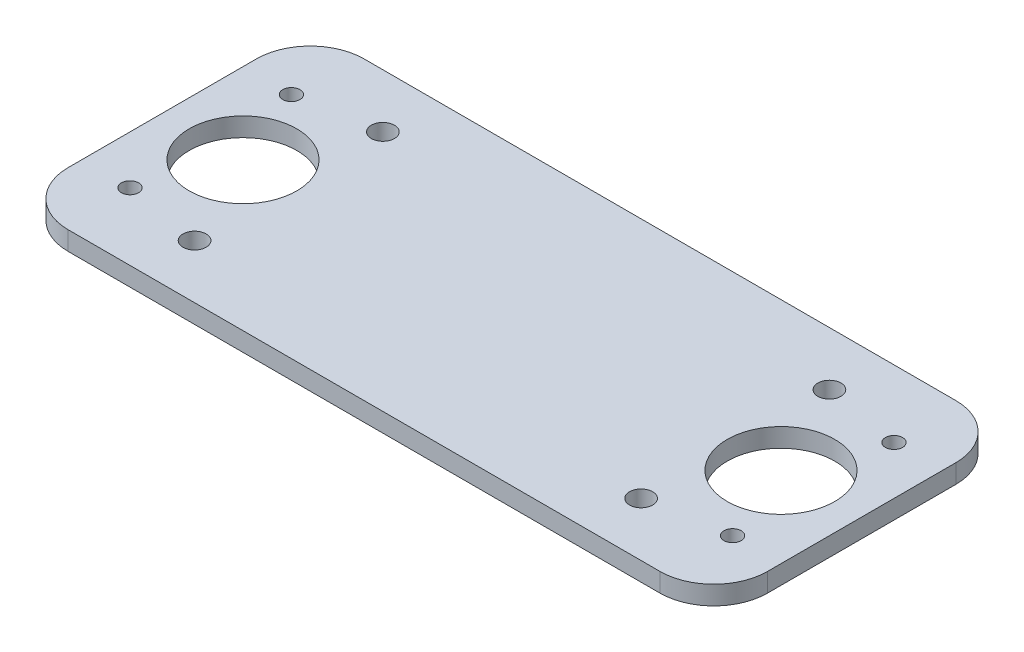
SolidWorks part; units mm, degrees
ref_plane "Front Plane" through (0, 0, 0) normal (0, 0, 1) x (1, 0, 0)
ref_plane "Top Plane" through (0, 0, 0) normal (0, 1, 0) x (1, 0, 0)
ref_plane "Right Plane" through (0, 0, 0) normal (1, 0, 0) x (0, 0, -1)
sketch "Sketch1" plane through (0, 0, 0) normal (0, 1, 0) x (1, 0, 0)
  line L0 (65, 20.185) -> (65, -60.6934) construction
  line L1 (0, 0) -> (130, 0)
  line L2 (0, 0) -> (0, -55)
  line L3 (0, -55) -> (130, -55)
  line L4 (130, 0) -> (130, -55)
  line L5 (-10.4412, -27.5) -> (139.8504, -27.5) construction
  circle A0 centre (9, -12.5) radius 1.6
  circle A1 centre (9, -42.5) radius 1.6
  circle A4 centre (121, -42.5) radius 1.6
  circle A7 centre (121, -12.5) radius 1.6
  circle A12 centre (15, -27.5) radius 10
  circle A13 centre (115, -27.5) radius 10
  circle A14 centre (106.5, -10) radius 2.15
  circle A15 centre (106.5, -45) radius 2.15
  circle A16 centre (23.5, -45) radius 2.15
  circle A17 centre (23.5, -10) radius 2.15
  dimension "D3" = 3.2
  dimension "D4" = 3.2
  dimension "D5" = 35
  dimension "D6" = 17.5
  dimension "D13" = 17.5
  dimension "D25" = 20
  dimension "D27" = 20
  dimension "D8" = 4.3
  dimension "D9" = 4.3
  dimension "D1" = 130
  dimension "D2" = 55
  dimension "D7" = 30
  dimension "D10" = 41.5
  dimension "D11" = 65
  dimension "D12" = 9
  dimension "D26" = 15
  dimension "D28" = 15
extrude "Boss-Extrude2" add sketch "Sketch1" along normal blind 3.5
fillet "Fillet2" radius 10 4 edges at (0, 1.75, 0) (0, 1.75, 55) (130, 1.75, 55) (130, 1.75, 0)
